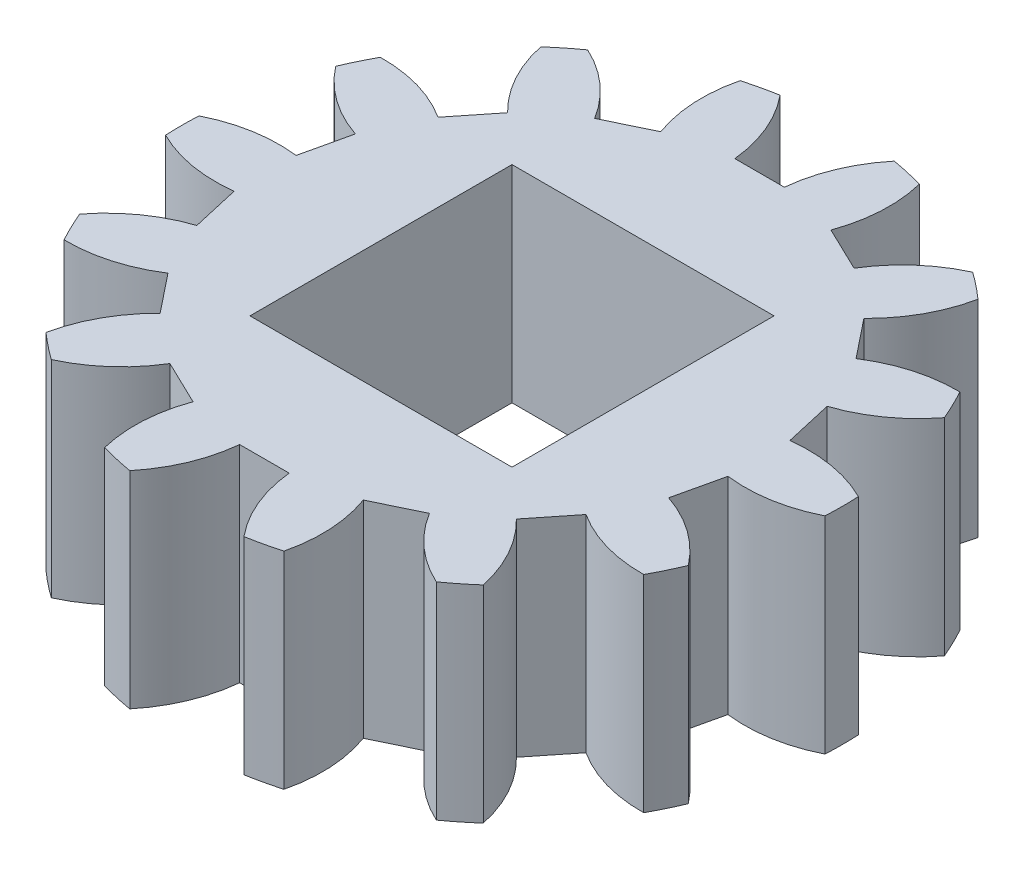
SolidWorks part; units mm, degrees
material "ABS"
ref_plane "Front Plane" through (0, 0, 0) normal (0, 0, 1) x (1, 0, 0)
ref_plane "Top Plane" through (0, 0, 0) normal (0, 1, 0) x (1, 0, 0)
ref_plane "Right Plane" through (0, 0, 0) normal (1, 0, 0) x (0, 0, -1)
sketch "Sketch3" plane through (0, 0, 0) normal (0, 1, 0) x (1, 0, 0)
  circle A2 centre (0, 0) radius 8
  dimension "D1" = 16
extrude "Boss-Extrude3" add sketch "Sketch3" along normal blind 5
sketch "Sketch4" plane through (0, 5, 0) normal (0, 1, 0) x (1, 0, 0)
  line L0 (-0.6, 6) -> (0.6, 6)
  line L1 (0, 0) -> (0, 6) construction
  line L2 (0, 6) -> (0, 8) construction
  line L3 (0, 0) -> (-0.6, 6) construction
  line L4 (0, 0) -> (0.6, 6) construction
  line L5 (2.0627, 5.6661) -> (3.1439, 5.1455)
  line L6 (4.3169, 4.21) -> (5.0651, 3.2718)
  line L7 (5.7161, 1.9201) -> (5.9831, 0.7502)
  line L8 (5.9831, -0.7502) -> (5.7161, -1.9201)
  line L9 (5.0651, -3.2718) -> (4.3169, -4.21)
  line L10 (3.1439, -5.1455) -> (2.0627, -5.6661)
  line L11 (0.6, -6) -> (-0.6, -6)
  line L12 (-2.0627, -5.6661) -> (-3.1439, -5.1455)
  line L13 (-4.3169, -4.21) -> (-5.0651, -3.2718)
  line L14 (-5.7161, -1.9201) -> (-5.9831, -0.7502)
  line L15 (-5.9831, 0.7502) -> (-5.7161, 1.9201)
  line L16 (-5.0651, 3.2718) -> (-4.3169, 4.21)
  line L17 (-3.1439, 5.1455) -> (-2.0627, 5.6661)
  arc A0 (-1.3832, 7.8795) -> (-0.6, 6) centre (-4.0826, 5.6517) cw
  circle A1 centre (0, 0) radius 8 construction
  arc A2 (0.6, 6) -> (1.3832, 7.8795) centre (4.0826, 5.6517) cw
  arc A4 (-1.3832, 7.8795) -> (1.3832, 7.8795) centre (0, 0) cw
  arc A5 (2.1726, 7.6993) -> (2.0627, 5.6661) centre (-1.2261, 6.8634) cw
  arc A6 (2.1726, 7.6993) -> (4.665, 6.4991) centre (0, 0) cw
  arc A7 (3.1439, 5.1455) -> (4.665, 6.4991) centre (6.1305, 3.3207) cw
  arc A8 (5.2981, 5.9942) -> (4.3169, 4.21) centre (1.8732, 6.7157) cw
  arc A9 (5.2981, 5.9942) -> (7.0229, 3.8314) centre (0, 0) cw
  arc A10 (5.0651, 3.2718) -> (7.0229, 3.8314) centre (6.9642, 0.3319) cw
  arc A11 (7.3742, 3.1019) -> (5.7161, 1.9201) centre (4.6016, 5.2379) cw
  arc A12 (7.3742, 3.1019) -> (7.9897, 0.4049) centre (0, 0) cw
  arc A13 (5.9831, 0.7502) -> (7.9897, 0.4049) centre (6.4185, -2.7226) cw
  arc A14 (7.9897, -0.4049) -> (5.9831, -0.7502) centre (6.4185, 2.7226) cw
  arc A15 (7.9897, -0.4049) -> (7.3742, -3.1019) centre (0, 0) cw
  arc A16 (5.7161, -1.9201) -> (7.3742, -3.1019) centre (4.6016, -5.2379) cw
  arc A17 (7.0229, -3.8314) -> (5.0651, -3.2718) centre (6.9642, -0.3319) cw
  arc A18 (7.0229, -3.8314) -> (5.2981, -5.9942) centre (0, 0) cw
  arc A19 (4.3169, -4.21) -> (5.2981, -5.9942) centre (1.8732, -6.7157) cw
  arc A20 (4.665, -6.4991) -> (3.1439, -5.1455) centre (6.1305, -3.3207) cw
  arc A21 (4.665, -6.4991) -> (2.1726, -7.6993) centre (0, 0) cw
  arc A22 (2.0627, -5.6661) -> (2.1726, -7.6993) centre (-1.2261, -6.8634) cw
  arc A23 (1.3832, -7.8795) -> (0.6, -6) centre (4.0826, -5.6517) cw
  arc A24 (1.3832, -7.8795) -> (-1.3832, -7.8795) centre (0, 0) cw
  arc A25 (-0.6, -6) -> (-1.3832, -7.8795) centre (-4.0826, -5.6517) cw
  arc A26 (-2.1726, -7.6993) -> (-2.0627, -5.6661) centre (1.2261, -6.8634) cw
  arc A27 (-2.1726, -7.6993) -> (-4.665, -6.4991) centre (0, 0) cw
  arc A28 (-3.1439, -5.1455) -> (-4.665, -6.4991) centre (-6.1305, -3.3207) cw
  arc A29 (-5.2981, -5.9942) -> (-4.3169, -4.21) centre (-1.8732, -6.7157) cw
  arc A30 (-5.2981, -5.9942) -> (-7.0229, -3.8314) centre (0, 0) cw
  arc A31 (-5.0651, -3.2718) -> (-7.0229, -3.8314) centre (-6.9642, -0.3319) cw
  arc A32 (-7.3742, -3.1019) -> (-5.7161, -1.9201) centre (-4.6016, -5.2379) cw
  arc A33 (-7.3742, -3.1019) -> (-7.9897, -0.4049) centre (0, 0) cw
  arc A34 (-5.9831, -0.7502) -> (-7.9897, -0.4049) centre (-6.4185, 2.7226) cw
  arc A35 (-7.9897, 0.4049) -> (-5.9831, 0.7502) centre (-6.4185, -2.7226) cw
  arc A36 (-7.9897, 0.4049) -> (-7.3742, 3.1019) centre (0, 0) cw
  arc A37 (-5.7161, 1.9201) -> (-7.3742, 3.1019) centre (-4.6016, 5.2379) cw
  arc A38 (-7.0229, 3.8314) -> (-5.0651, 3.2718) centre (-6.9642, 0.3319) cw
  arc A39 (-7.0229, 3.8314) -> (-5.2981, 5.9942) centre (0, 0) cw
  arc A40 (-4.3169, 4.21) -> (-5.2981, 5.9942) centre (-1.8732, 6.7157) cw
  arc A41 (-4.665, 6.4991) -> (-3.1439, 5.1455) centre (-6.1305, 3.3207) cw
  arc A42 (-4.665, 6.4991) -> (-2.1726, 7.6993) centre (0, 0) cw
  arc A43 (-2.0627, 5.6661) -> (-2.1726, 7.6993) centre (1.2261, 6.8634) cw
  point P70 (0, 0)
  point P96 (0, 0)
  dimension "D2" = 3.5
  dimension "D1" = 2
  dimension "D3" = 1.2
  dimension "D4" = 14
extrude "Cut-Extrude1" cut sketch "Sketch4" against normal through all
sketch "Sketch5" plane through (0, 5, 0) normal (0, 1, 0) x (1, 0, 0)
  line L3 (-3.175, -3.175) -> (3.175, -3.175)
  line L4 (-3.175, -3.175) -> (-3.175, 3.175)
  line L5 (-3.175, 3.175) -> (3.175, 3.175)
  line L6 (3.175, -3.175) -> (3.175, 3.175)
  line L7 (-3.175, -3.175) -> (3.175, 3.175) construction
  line L8 (-3.175, 3.175) -> (3.175, -3.175) construction
  point P0 (0, 0)
  dimension "D1" = 6.35
extrude "Cut-Extrude2" cut sketch "Sketch5" against normal through all
sketch "Sketch6" plane through (0, 5, 0) normal (0, 1, 0) x (1, 0, 0)
  circle A0 centre (0, 0) radius 7
  dimension "D1" = 14
